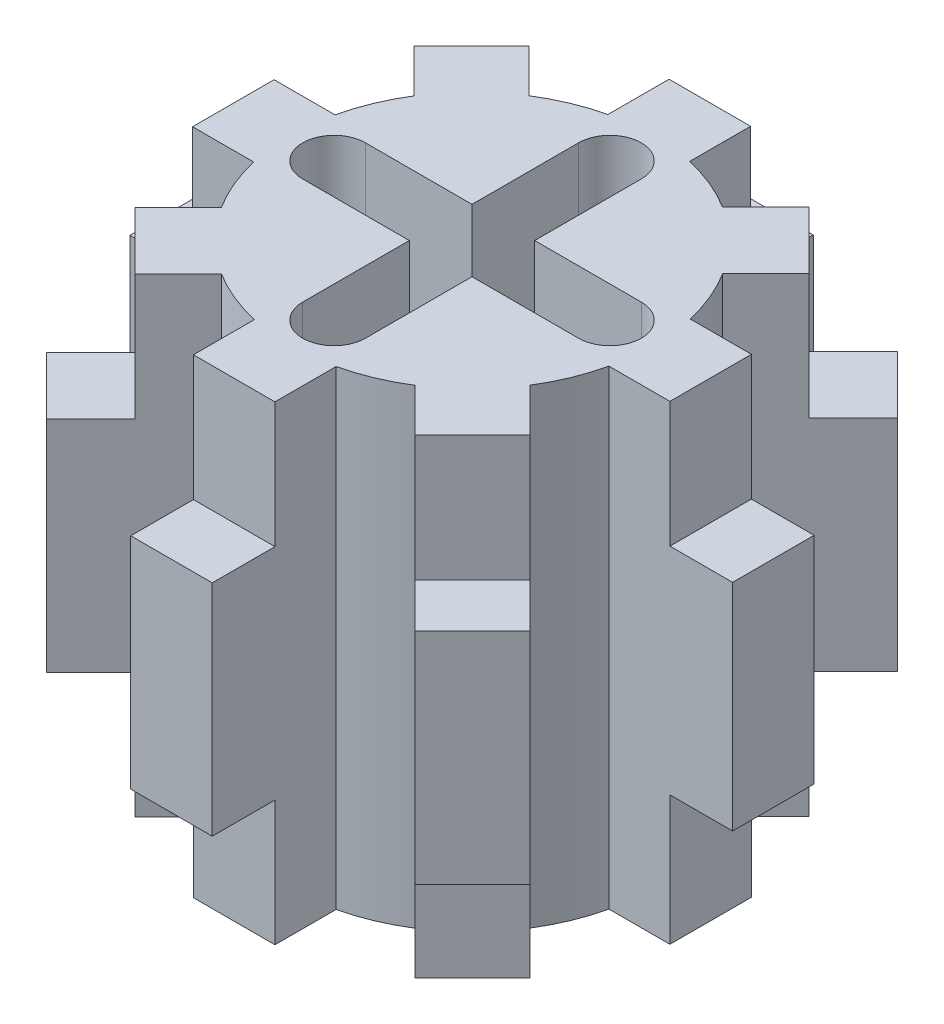
SolidWorks part; units mm, degrees
ref_plane "Front Plane" through (0, 0, 0) normal (0, 0, 1) x (1, 0, 0)
ref_plane "Top Plane" through (0, 0, 0) normal (0, 1, 0) x (1, 0, 0)
ref_plane "Right Plane" through (0, 0, 0) normal (1, 0, 0) x (0, 0, -1)
sketch "Sketch1" plane through (0, 0, 0) normal (0, 1, 0) x (1, 0, 0)
  circle A0 centre (0, 0) radius 2.9
  circle A1 centre (0, 0) radius 2.75
  dimension "D1" = 5.8
  dimension "D2" = 5.5
extrude "Boss-Extrude1" add sketch "Sketch1" along normal blind 7.5 contours A0
sketch "Sketch2" plane through (0, 0, 0) normal (0, -1, 0) x (1, 0, 0)
  line L0 (0, 2.75) -> (0, 2.2) construction
  line L1 (0, -2.75) -> (0, -2.2) construction
  line L2 (0, 2.2) -> (0, -2.2) construction
  line L3 (0.5, 2.2) -> (0.5, -2.2)
  line L4 (-0.5, 2.2) -> (-0.5, -2.2)
  line L5 (-2.75, 0) -> (-2.2, 0) construction
  line L6 (2.75, 0) -> (2.2, 0) construction
  line L7 (2.2, 0) -> (-2.2, 0) construction
  line L8 (2.2, -0.5) -> (-2.2, -0.5)
  line L9 (2.2, 0.5) -> (-2.2, 0.5)
  circle A0 centre (0, 0) radius 2.75
  arc A1 (0.5, 2.2) -> (-0.5, 2.2) centre (0, 2.2) ccw
  arc A2 (-0.5, -2.2) -> (0.5, -2.2) centre (0, -2.2) ccw
  arc A3 (2.2, -0.5) -> (2.2, 0.5) centre (2.2, 0) ccw
  arc A4 (-2.2, 0.5) -> (-2.2, -0.5) centre (-2.2, 0) ccw
  point P7 (0, 0)
  point P16 (0, 0)
  dimension "D1" = 5.5
  dimension "D3" = 0.55
  dimension "D2" = 0.55
extrude "Cut-Extrude1" cut sketch "Sketch2" against normal blind 7.5 contours L3 A1 L4 L9 | L3 L9 L4 L8 | L4 A2 L3 L8 | L8 A3 L9 L3 | L9 A4 L8 L4
ref_plane "Plane2" through (2.8, 0, 0) normal (1, 0, 0) x (0, 0, -1)
ref_plane "Plane3" through (0, 0, 2.8) normal (0, 0, 1) x (1, 0, 0)
sketch "Sketch8" plane through (2.8, 0, 0) normal (1, 0, 0) x (0, 0, -1)
  line L5 (0, 7.5) -> (0.6567, 7.5) construction
  line L6 (0.5, 7.5) -> (-0.5, 7.5) construction
  line L7 (2.9, 7.5) -> (-2.9, 7.5) construction
  line L8 (-2.9, 0) -> (2.9, 0) construction
  line L9 (0.6567, 7.5) -> (-0.6433, 7.5)
  line L10 (0.6567, 7.5) -> (0.6567, 0)
  line L11 (0.6567, 0) -> (-0.6433, 0)
  line L12 (-0.6433, 7.5) -> (-0.6433, 0)
  dimension "D1" = 1.3
extrude "Boss-Extrude4" add sketch "Sketch8" along normal blind 1
pattern_circular "CirPattern3" count 8 over 360 about axis through (0, 0, 0) along (0, 1, 0) of "Boss-Extrude4"
sketch "Sketch10" plane through (0, 0, -3.8) normal (0, 0, -1) x (-1, 0, 0)
  line L0 (0.0067, 7.5) -> (0.0067, 5.5) construction
  line L1 (0.6567, 7.5) -> (-0.6433, 7.5) construction
  line L2 (0, 0) -> (0, 2) construction
  line L3 (-0.6433, 7.5) -> (-0.6433, 0) construction
  line L4 (-0.6433, 5.5) -> (0.6567, 5.5)
  line L5 (-0.6433, 5.5) -> (-0.6433, 2)
  line L6 (-0.6433, 2) -> (0.6567, 2)
  line L7 (0.6567, 5.5) -> (0.6567, 2)
  line L8 (0.6567, 0) -> (0.6567, 7.5) construction
extrude "Boss-Extrude6" add sketch "Sketch10" along normal blind 1
sketch "Sketch11" plane through (-2.687, 0, -2.687) normal (-0.7071, 0, -0.7071) x (-0.7071, 0, 0.7071)
  line L0 (0.0067, 7.5) -> (0.0067, 5.5) construction
  line L1 (0.6567, 7.5) -> (-0.6433, 7.5) construction
  line L2 (0, 0) -> (0, 2) construction
  line L3 (-0.6433, 7.5) -> (-0.6433, 0) construction
  line L4 (-0.6433, 5.5) -> (0.6567, 5.5)
  line L5 (-0.6433, 5.5) -> (-0.6433, 2)
  line L6 (-0.6433, 2) -> (0.6567, 2)
  line L7 (0.6567, 5.5) -> (0.6567, 2)
  line L8 (0.6567, 0) -> (0.6567, 7.5) construction
  dimension "D1" = 2
  dimension "D2" = 3.5
extrude "Boss-Extrude7" add sketch "Sketch11" along normal blind 1
sketch "Sketch12" plane through (-3.8, 0, 0) normal (-1, 0, 0) x (0, 0, 1)
  line L0 (0.0067, 7.5) -> (0.0067, 5.5) construction
  line L1 (0.6567, 7.5) -> (-0.6433, 7.5) construction
  line L2 (0, 0) -> (0, 2) construction
  line L3 (-0.6433, 7.5) -> (-0.6433, 0) construction
  line L4 (-0.6433, 5.5) -> (0.6567, 5.5)
  line L5 (-0.6433, 5.5) -> (-0.6433, 2)
  line L6 (-0.6433, 2) -> (0.6567, 2)
  line L7 (0.6567, 5.5) -> (0.6567, 2)
  line L8 (0.6567, 0) -> (0.6567, 7.5) construction
  dimension "D1" = 2
  dimension "D2" = 2
  dimension "D3" = 3.5
extrude "Boss-Extrude8" add sketch "Sketch12" along normal blind 1
sketch "Sketch14" plane through (-2.687, 0, 2.687) normal (-0.7071, 0, 0.7071) x (0.7071, 0, 0.7071)
  line L0 (0.0067, 7.5) -> (0.0067, 5.5) construction
  line L1 (0.6567, 7.5) -> (-0.6433, 7.5) construction
  line L2 (0, 0) -> (0, 2) construction
  line L3 (-0.6433, 7.5) -> (-0.6433, 0) construction
  line L4 (-0.6433, 2) -> (0.6567, 2)
  line L5 (-0.6433, 2) -> (-0.6433, 5.5)
  line L6 (-0.6433, 5.5) -> (0.6567, 5.5)
  line L7 (0.6567, 2) -> (0.6567, 5.5)
  line L8 (0.6567, 0) -> (0.6567, 7.5) construction
  dimension "D1" = 2
extrude "Boss-Extrude9" add sketch "Sketch14" along normal blind 1
sketch "Sketch15" plane through (0, 0, 3.8) normal (0, 0, 1) x (1, 0, 0)
  line L0 (0.0067, 7.5) -> (0.0067, 5.5) construction
  line L1 (0.6567, 7.5) -> (-0.6433, 7.5) construction
  line L2 (0.0067, 0) -> (0.0067, 2) construction
  line L3 (-0.6433, 0) -> (0.6567, 0) construction
  line L4 (-0.6433, 7.5) -> (-0.6433, 0) construction
  line L5 (-0.6433, 5.5) -> (0.6567, 5.5)
  line L6 (-0.6433, 5.5) -> (-0.6433, 2)
  line L7 (-0.6433, 2) -> (0.6567, 2)
  line L8 (0.6567, 5.5) -> (0.6567, 2)
  line L9 (0.6567, 0) -> (0.6567, 7.5) construction
  dimension "D1" = 2
extrude "Boss-Extrude10" add sketch "Sketch15" along normal blind 1
sketch "Sketch16" plane through (2.687, 0, 2.687) normal (0.7071, 0, 0.7071) x (0.7071, 0, -0.7071)
  line L0 (0.0067, 7.5) -> (0.0067, 5.5) construction
  line L1 (0.6567, 7.5) -> (-0.6433, 7.5) construction
  line L2 (0, 0) -> (0, 2) construction
  line L3 (-0.6433, 7.5) -> (-0.6433, 0) construction
  line L4 (-0.6433, 5.5) -> (0.6567, 5.5)
  line L5 (-0.6433, 5.5) -> (-0.6433, 2)
  line L6 (-0.6433, 2) -> (0.6567, 2)
  line L7 (0.6567, 5.5) -> (0.6567, 2)
  line L8 (0.6567, 0) -> (0.6567, 7.5) construction
  dimension "D1" = 2
extrude "Boss-Extrude11" add sketch "Sketch16" along normal blind 1
sketch "Sketch17" plane through (3.8, 0, 0) normal (1, 0, 0) x (0, 0, -1)
  line L0 (0.0067, 7.5) -> (0.0067, 5.5) construction
  line L1 (0.6567, 7.5) -> (-0.6433, 7.5) construction
  line L2 (0, 0) -> (0, 2) construction
  line L3 (-0.6433, 7.5) -> (-0.6433, 0) construction
  line L4 (-0.6433, 5.5) -> (0.6567, 5.5)
  line L5 (-0.6433, 5.5) -> (-0.6433, 2.0649)
  line L6 (-0.6433, 2.0649) -> (0.6567, 2.0649)
  line L7 (0.6567, 5.5) -> (0.6567, 2.0649)
  line L8 (0.6567, 0) -> (0.6567, 7.5) construction
  dimension "D1" = 2
  dimension "D2" = 2
extrude "Boss-Extrude12" add sketch "Sketch17" along normal blind 1
sketch "Sketch18" plane through (2.687, 0, -2.687) normal (0.7071, 0, -0.7071) x (-0.7071, 0, -0.7071)
  line L0 (0.0067, 7.5) -> (0.0067, 5.5) construction
  line L1 (0.6567, 7.5) -> (-0.6433, 7.5) construction
  line L2 (0, 0) -> (0, 2) construction
  line L3 (-0.6433, 7.5) -> (-0.6433, 0) construction
  line L4 (-0.6433, 5.5) -> (0.6567, 5.5)
  line L5 (-0.6433, 5.5) -> (-0.6433, 2)
  line L6 (-0.6433, 2) -> (0.6567, 2)
  line L7 (0.6567, 5.5) -> (0.6567, 2)
  line L8 (0.6567, 0) -> (0.6567, 7.5) construction
extrude "Boss-Extrude13" add sketch "Sketch18" along normal blind 1
